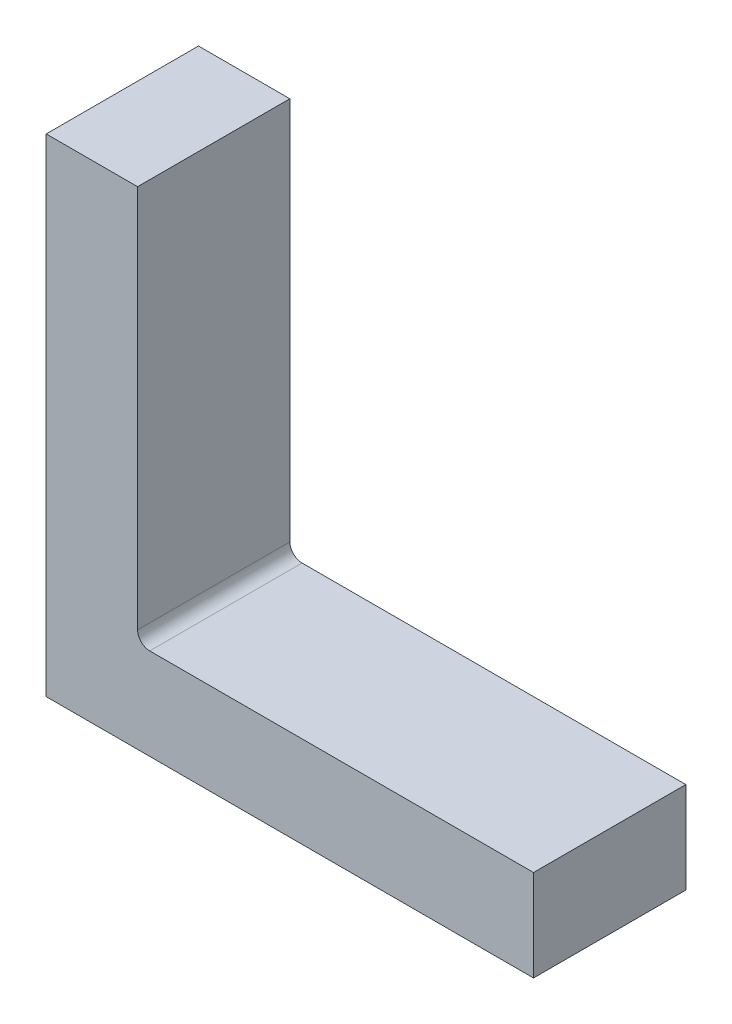
SolidWorks part; units mm, degrees
material "AISI 304"
ref_plane "Front" through (0, 0, 0) normal (0, 0, 1) x (1, 0, 0)
ref_plane "Top" through (0, 0, 0) normal (0, 1, 0) x (1, 0, 0)
ref_plane "Right" through (0, 0, 0) normal (1, 0, 0) x (0, 0, -1)
sketch "Sketch1" plane through (0, 0, 0) normal (0, 0, 1) x (1, 0, 0)
  line L0 (19.05, 101.6) -> (19.05, 19.05)
  line L1 (0, 0) -> (101.6, 0)
  line L2 (0, 0) -> (0, 101.6)
  line L3 (0, 101.6) -> (19.05, 101.6)
  line L4 (101.6, 0) -> (101.6, 19.05)
  line L5 (19.05, 19.05) -> (101.6, 19.05)
  dimension "D1" = 101.6
  dimension "D2" = 101.6
  dimension "D3" = 19.05
  dimension "D4" = 19.05
extrude "Extrude1" add sketch "Sketch1" along normal blind 31.75
fillet "Fillet1" radius 2.54 1 edges at (19.05, 19.05, 15.875)
